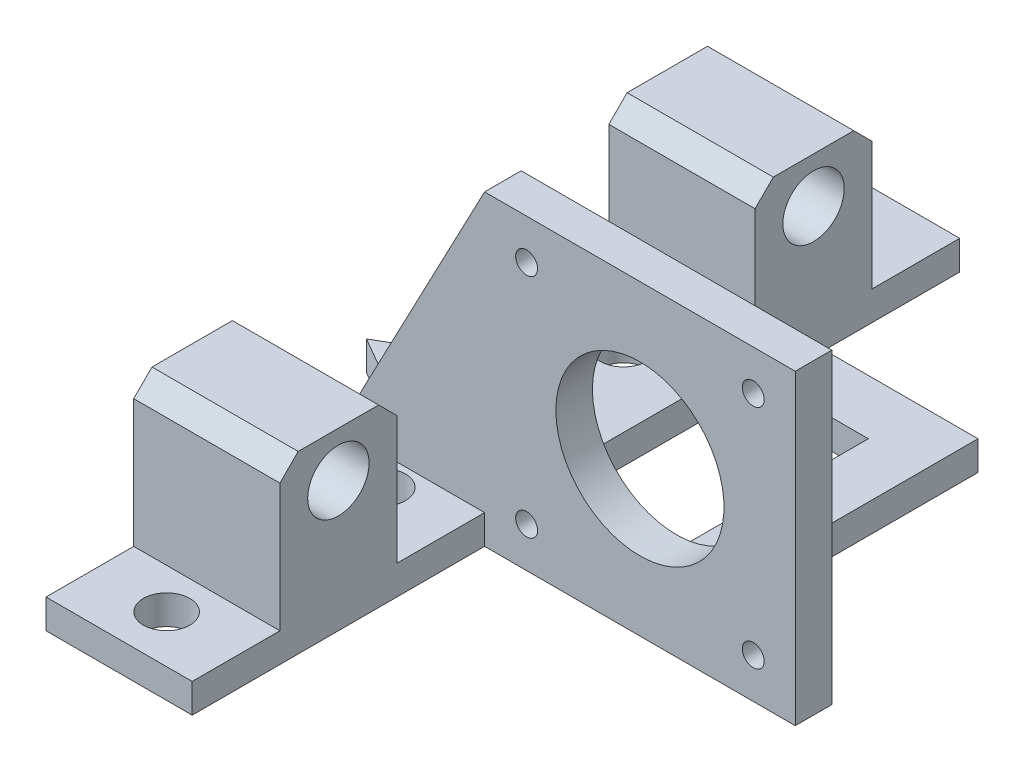
SolidWorks part; units mm, degrees
ref_plane "Front Plane" through (0, 0, 0) normal (0, 0, 1) x (1, 0, 0)
ref_plane "Top Plane" through (0, 0, 0) normal (0, 1, 0) x (1, 0, 0)
ref_plane "Right Plane" through (0, 0, 0) normal (1, 0, 0) x (0, 0, -1)
sketch "Sketch1" plane through (0, 0, 0) normal (0, 1, 0) x (1, 0, 0)
  line L1 (0, 0) -> (20, 0)
  line L2 (0, 0) -> (0, 105)
  line L3 (0, 105) -> (20, 105)
  line L4 (20, 0) -> (20, 105)
  dimension "D1" = 105
  dimension "D2" = 20
extrude "Boss-Extrude1" add sketch "Sketch1" along normal blind 4
sketch "Sketch2" plane through (0, 0, 0) normal (-1, 0, 0) x (0, 0, 1)
  line L0 (-105, 0) -> (0, 0) construction
  line L5 (-12, 21.5) -> (-14.5, 24)
  line L6 (-93, 0) -> (-77, 0)
  line L7 (-93, 0) -> (-93, 24)
  line L8 (-93, 24) -> (-77, 24)
  line L9 (-77, 0) -> (-77, 24)
  line L10 (-105, 0) -> (-93, 0) construction
  line L11 (-79.5, 24) -> (-77, 21.5)
  line L12 (-93, 21.5) -> (-90.5, 24)
  line L13 (-52.5, 0) -> (-52.5, 4) construction
  line L14 (-25.5, 24) -> (-28, 21.5)
  line L15 (-105, 4) -> (0, 4) construction
  line L16 (-28, 0) -> (-28, 24)
  line L17 (-12, 24) -> (-28, 24)
  line L18 (-12, 0) -> (-12, 24)
  line L19 (-12, 0) -> (-28, 0)
  circle A0 centre (-85, 17.8) radius 4.2
  circle A1 centre (-20, 17.8) radius 4.2
  point P10 (-85, 24)
  point P25 (-52.5, 4)
  point P30 (-20, 24)
  line M15 (0, 4) -> (-105, 4)
  dimension "D4" = 8.4
  dimension "D2" = 16
  dimension "D3" = 24
  dimension "D6" = 2.5
  dimension "D7" = 2.5
  dimension "D8" = 2.5
  dimension "D9" = 2.5
  dimension "D1" = 65
  dimension "D5" = 6.2
extrude "Boss-Extrude2" add sketch "Sketch2" against normal up to surface (20 mm away) contours L18 L5 L17 L14 L16 A1 M15 | L12 L7 L9 L11 L8 A0 M15 up to face at (20, 2, -52.5)
sketch "Sketch3" plane through (0, 0, 0) normal (0, -1, 0) x (1, 0, 0)
  line L0 (0, -57.5) -> (-8.6603, -52.5)
  line L1 (0, -105) -> (0, 0) construction
  line L2 (-8.6603, -52.5) -> (0, -47.5)
  line L3 (0, -57.5) -> (0, -47.5)
  point P6 (0, -52.5)
  dimension "D1" = 10
  dimension "D2" = 10
  dimension "D3" = 10
extrude "Boss-Extrude3" add sketch "Sketch3" against normal up to surface (4 mm away) up to face at (10, 4, -99)
sketch "Sketch4" plane through (0, 4, 0) normal (0, 1, 0) x (1, 0, 0)
  line L0 (10, 105) -> (10, 0) construction
  line L1 (20, 105) -> (0, 105) construction
  line L2 (0, 0) -> (20, 0) construction
  circle A0 centre (10, 98.5) radius 3.175
  circle A1 centre (10, 69) radius 3.175
  circle A2 centre (10, 36) radius 3.175
  circle A3 centre (10, 6.5) radius 3.175
  dimension "D1" = 6.35
  dimension "D2" = 6.5
  dimension "D3" = 36
  dimension "D4" = 6.5
  dimension "D5" = 36
extrude "Cut-Extrude1" cut sketch "Sketch4" against normal through all
sketch "Sketch5" plane through (20, 0, 0) normal (1, 0, 0) x (0, 0, -1)
  line L0 (0, 0) -> (105, 0) construction
  line L1 (45, 0) -> (40, 0)
  line L2 (45, 0) -> (45, 42)
  line L3 (45, 42) -> (40, 42)
  line L4 (40, 0) -> (40, 42)
  dimension "D1" = 42
  dimension "D2" = 5
  dimension "D3" = 7.5
extrude "Boss-Extrude4" add sketch "Sketch5" along normal blind 42.5
sketch "Sketch6" plane through (0, 0, -45) normal (0, 0, -1) x (-1, 0, 0)
  line L0 (-41.25, 42) -> (-41.25, 0) construction
  line L1 (-62.5, 42) -> (-20, 42) construction
  line L2 (-62.5, 0) -> (-20, 0) construction
  line L3 (-62.5, 21) -> (-20, 21) construction
  line L4 (-62.5, 0) -> (-62.5, 42) construction
  line L5 (-20, 4) -> (-20, 42) construction
  circle A0 centre (-41.25, 21) radius 11.5
  circle A1 centre (-56.75, 36.5) radius 1.5
  circle A5 centre (-25.75, 36.5) radius 1.5
  circle A6 centre (-25.75, 5.5) radius 1.5
  circle A7 centre (-56.75, 5.5) radius 1.5
  dimension "D3" = 3
  dimension "D4" = 23
  dimension "D1" = 15.5
  dimension "D2" = 15.5
extrude "Cut-Extrude2" cut sketch "Sketch6" against normal through all
sketch "Sketch7" plane through (0, 0, -40) normal (0, 0, 1) x (1, 0, 0)
  line L0 (20, 42) -> (0, 4)
  line L1 (0, 4) -> (20, 4)
  line L2 (20, 4) -> (20, 42)
extrude "Boss-Extrude5" add sketch "Sketch7" against normal up to surface (5 mm away) up to face at (58.25, 5.5, -45)
sketch "Sketch8" plane through (0, 0, 0) normal (0, -1, 0) x (1, 0, 0)
  line L0 (45, -45) -> (45, -82.5)
  line L1 (62.5, -45) -> (20, -45) construction
  line L2 (45, -82.5) -> (20, -82.5)
  line L3 (20, -45) -> (20, -105) construction
  line L4 (20, -82.5) -> (20, -75)
  line L5 (20, -75) -> (37.5, -75)
  line L6 (37.5, -75) -> (37.5, -45)
  line L7 (37.5, -45) -> (45, -45)
  point P11 (41.25, -45)
  point P12 (41.25, -45)
  dimension "D1" = 7.5
extrude "Boss-Extrude6" add sketch "Sketch8" against normal up to surface (4 mm away) up to face at (10, 4, -3.325)
equation "\"8mm hole\" = 8.4mm"
equation "\"D4@Sketch2\"= \"8mm hole\""
equation "\"22mm hole\"= 23mm"
equation "\"15mm hole\"= 15.8mm"
equation "\"bed height offset\"= 3mm"
equation "\"D3@Sketch2\"= 21 + \"bed height offset\""
equation "\"D4@Sketch6\"= \"22mm hole\""
